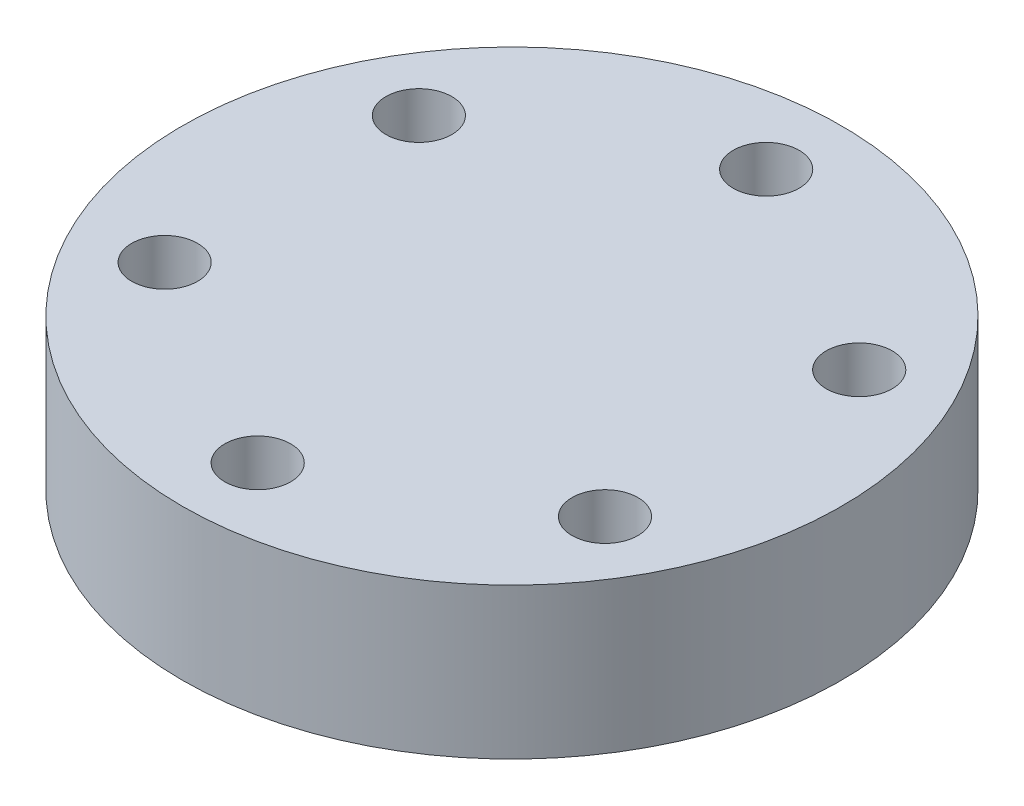
SolidWorks part; units mm, degrees
ref_plane "前视基准面" through (0, 0, 0) normal (0, 0, 1) x (1, 0, 0)
ref_plane "上视基准面" through (0, 0, 0) normal (0, 1, 0) x (1, 0, 0)
ref_plane "右视基准面" through (0, 0, 0) normal (1, 0, 0) x (0, 0, -1)
sketch "草图1" plane through (0, 0, 0) normal (0, 1, 0) x (1, 0, 0)
  circle A0 centre (0, 0) radius 17.5
  dimension "D1" = 35
extrude "凸台-拉伸1" add sketch "草图1" along normal blind 8
sketch "草图2" plane through (0, 8, 0) normal (0, 1, 0) x (1, 0, 0)
  circle A0 centre (0, 0) radius 13.5 construction
  circle A1 centre (0, 13.5) radius 1.75
  circle A2 centre (11.6913, 6.75) radius 1.75
  circle A3 centre (11.6913, -6.75) radius 1.75
  circle A4 centre (0, -13.5) radius 1.75
  circle A5 centre (-11.6913, -6.75) radius 1.75
  circle A6 centre (-11.6913, 6.75) radius 1.75
  point P17 (0, 0)
  dimension "D1" = 27
  dimension "D2" = 3.5
  dimension "D3" = 6
extrude "切除-拉伸1" cut sketch "草图2" against normal blind 14
